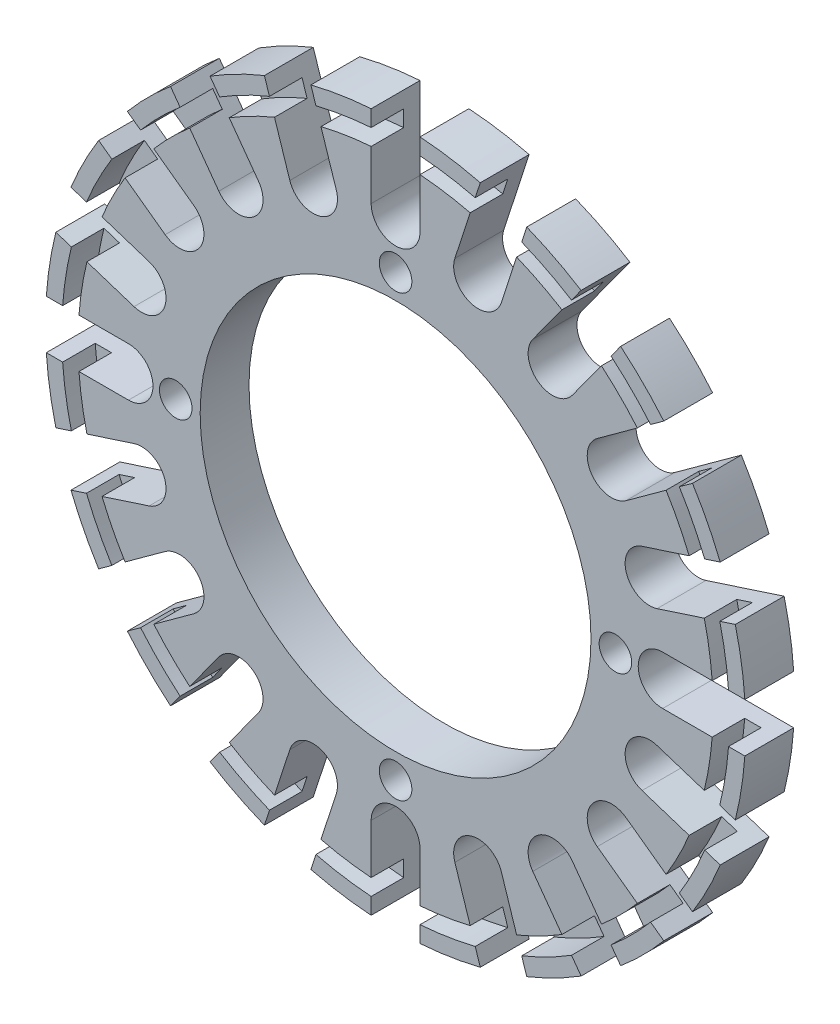
SolidWorks part; units mm, degrees
ref_plane "Front" through (0, 0, 0) normal (0, 0, 1) x (1, 0, 0)
ref_plane "Top" through (0, 0, 0) normal (0, 1, 0) x (1, 0, 0)
ref_plane "Right" through (0, 0, 0) normal (1, 0, 0) x (0, 0, -1)
sketch "Sketch1" plane through (0, 0, 0) normal (0, 0, 1) x (1, 0, 0)
  line L2 (-1.5, 16.4) -> (-1.5, 21.4476)
  line L5 (1.5, 21.4476) -> (1.5, 16.4)
  line L6 (8.0543, 19.9344) -> (6.4945, 15.1338)
  line L7 (3.6413, 16.0609) -> (5.2011, 20.8614)
  line L8 (13.8201, 16.4698) -> (10.8532, 12.3862)
  line L9 (8.4262, 14.1496) -> (11.3931, 18.2332)
  line L10 (18.2332, 11.3931) -> (14.1496, 8.4262)
  line L11 (12.3862, 10.8532) -> (16.4698, 13.8201)
  line L12 (20.8614, 5.2011) -> (16.0609, 3.6413)
  line L13 (15.1338, 6.4945) -> (19.9344, 8.0543)
  line L14 (21.4476, -1.5) -> (16.4, -1.5)
  line L15 (16.4, 1.5) -> (21.4476, 1.5)
  line L16 (19.9344, -8.0543) -> (15.1338, -6.4945)
  line L17 (16.0609, -3.6413) -> (20.8614, -5.2011)
  line L18 (16.4698, -13.8201) -> (12.3862, -10.8532)
  line L19 (14.1496, -8.4262) -> (18.2332, -11.3931)
  line L20 (11.3931, -18.2332) -> (8.4262, -14.1496)
  line L21 (10.8532, -12.3862) -> (13.8201, -16.4698)
  line L22 (5.2011, -20.8614) -> (3.6413, -16.0609)
  line L23 (6.4945, -15.1338) -> (8.0543, -19.9344)
  line L24 (-1.5, -21.4476) -> (-1.5, -16.4)
  line L25 (1.5, -16.4) -> (1.5, -21.4476)
  line L26 (-8.0543, -19.9344) -> (-6.4945, -15.1338)
  line L27 (-3.6413, -16.0609) -> (-5.2011, -20.8614)
  line L28 (-13.8201, -16.4698) -> (-10.8532, -12.3862)
  line L29 (-8.4262, -14.1496) -> (-11.3931, -18.2332)
  line L30 (-18.2332, -11.3931) -> (-14.1496, -8.4262)
  line L31 (-12.3862, -10.8532) -> (-16.4698, -13.8201)
  line L32 (-20.8614, -5.2011) -> (-16.0609, -3.6413)
  line L33 (-15.1338, -6.4945) -> (-19.9344, -8.0543)
  line L34 (-21.4476, 1.5) -> (-16.4, 1.5)
  line L35 (-16.4, -1.5) -> (-21.4476, -1.5)
  line L36 (-19.9344, 8.0543) -> (-15.1338, 6.4945)
  line L37 (-16.0609, 3.6413) -> (-20.8614, 5.2011)
  line L38 (-16.4698, 13.8201) -> (-12.3862, 10.8532)
  line L39 (-14.1496, 8.4262) -> (-18.2332, 11.3931)
  line L40 (-11.3931, 18.2332) -> (-8.4262, 14.1496)
  line L41 (-10.8532, 12.3862) -> (-13.8201, 16.4698)
  line L42 (-5.2011, 20.8614) -> (-3.6413, 16.0609)
  line L43 (-6.4945, 15.1338) -> (-8.0543, 19.9344)
  circle A0 centre (0, 0) radius 12
  circle A2 centre (0, 13.5) radius 1
  circle A5 centre (13.5, 0) radius 1
  circle A6 centre (0, -13.5) radius 1
  circle A7 centre (-13.5, 0) radius 1
  arc A11 (-1.5, 16.4) -> (1.5, 16.4) centre (0, 16.4) ccw
  arc A12 (-1.5, 21.4476) -> (-5.2011, 20.8614) centre (0, 0) ccw
  arc A13 (3.6413, 16.0609) -> (6.4945, 15.1338) centre (5.0679, 15.5973) ccw
  arc A14 (8.4262, 14.1496) -> (10.8532, 12.3862) centre (9.6397, 13.2679) ccw
  arc A15 (12.3862, 10.8532) -> (14.1496, 8.4262) centre (13.2679, 9.6397) ccw
  arc A16 (15.1338, 6.4945) -> (16.0609, 3.6413) centre (15.5973, 5.0679) ccw
  arc A17 (16.4, 1.5) -> (16.4, -1.5) centre (16.4, 0) ccw
  arc A18 (16.0609, -3.6413) -> (15.1338, -6.4945) centre (15.5973, -5.0679) ccw
  arc A19 (14.1496, -8.4262) -> (12.3862, -10.8532) centre (13.2679, -9.6397) ccw
  arc A20 (10.8532, -12.3862) -> (8.4262, -14.1496) centre (9.6397, -13.2679) ccw
  arc A21 (6.4945, -15.1338) -> (3.6413, -16.0609) centre (5.0679, -15.5973) ccw
  arc A22 (1.5, -16.4) -> (-1.5, -16.4) centre (0, -16.4) ccw
  arc A23 (-3.6413, -16.0609) -> (-6.4945, -15.1338) centre (-5.0679, -15.5973) ccw
  arc A24 (-8.4262, -14.1496) -> (-10.8532, -12.3862) centre (-9.6397, -13.2679) ccw
  arc A25 (-12.3862, -10.8532) -> (-14.1496, -8.4262) centre (-13.2679, -9.6397) ccw
  arc A26 (-15.1338, -6.4945) -> (-16.0609, -3.6413) centre (-15.5973, -5.0679) ccw
  arc A27 (-16.4, -1.5) -> (-16.4, 1.5) centre (-16.4, 0) ccw
  arc A28 (-16.0609, 3.6413) -> (-15.1338, 6.4945) centre (-15.5973, 5.0679) ccw
  arc A29 (-14.1496, 8.4262) -> (-12.3862, 10.8532) centre (-13.2679, 9.6397) ccw
  arc A30 (-10.8532, 12.3862) -> (-8.4262, 14.1496) centre (-9.6397, 13.2679) ccw
  arc A31 (-6.4945, 15.1338) -> (-3.6413, 16.0609) centre (-5.0679, 15.5973) ccw
  arc A32 (-8.0543, 19.9344) -> (-11.3931, 18.2332) centre (0, 0) ccw
  arc A33 (5.2011, 20.8614) -> (1.5, 21.4476) centre (0, 0) ccw
  arc A34 (11.3931, 18.2332) -> (8.0543, 19.9344) centre (0, 0) ccw
  arc A35 (16.4698, 13.8201) -> (13.8201, 16.4698) centre (0, 0) ccw
  arc A36 (19.9344, 8.0543) -> (18.2332, 11.3931) centre (0, 0) ccw
  arc A37 (21.4476, 1.5) -> (20.8614, 5.2011) centre (0, 0) ccw
  arc A38 (20.8614, -5.2011) -> (21.4476, -1.5) centre (0, 0) ccw
  arc A39 (18.2332, -11.3931) -> (19.9344, -8.0543) centre (0, 0) ccw
  arc A40 (13.8201, -16.4698) -> (16.4698, -13.8201) centre (0, 0) ccw
  arc A41 (8.0543, -19.9344) -> (11.3931, -18.2332) centre (0, 0) ccw
  arc A42 (1.5, -21.4476) -> (5.2011, -20.8614) centre (0, 0) ccw
  arc A43 (-5.2011, -20.8614) -> (-1.5, -21.4476) centre (0, 0) ccw
  arc A44 (-11.3931, -18.2332) -> (-8.0543, -19.9344) centre (0, 0) ccw
  arc A45 (-16.4698, -13.8201) -> (-13.8201, -16.4698) centre (0, 0) ccw
  arc A46 (-19.9344, -8.0543) -> (-18.2332, -11.3931) centre (0, 0) ccw
  arc A47 (-21.4476, -1.5) -> (-20.8614, -5.2011) centre (0, 0) ccw
  arc A48 (-20.8614, 5.2011) -> (-21.4476, 1.5) centre (0, 0) ccw
  arc A49 (-13.8201, 16.4698) -> (-16.4698, 13.8201) centre (0, 0) ccw
  arc A50 (-18.2332, 11.3931) -> (-19.9344, 8.0543) centre (0, 0) ccw
  dimension "D1" = 4
  dimension "D2" = 20
extrude "Boss-Extrude1" add sketch "Sketch1" along normal blind 3
sketch "Sketch2" plane through (0, 0, 3) normal (0, 0, 1) x (1, 0, 0)
  circle A0 centre (0, 0) radius 19.5
  circle A1 centre (0, 0) radius 20.5
extrude "Cut-Extrude1" cut sketch "Sketch2" against normal blind 2
